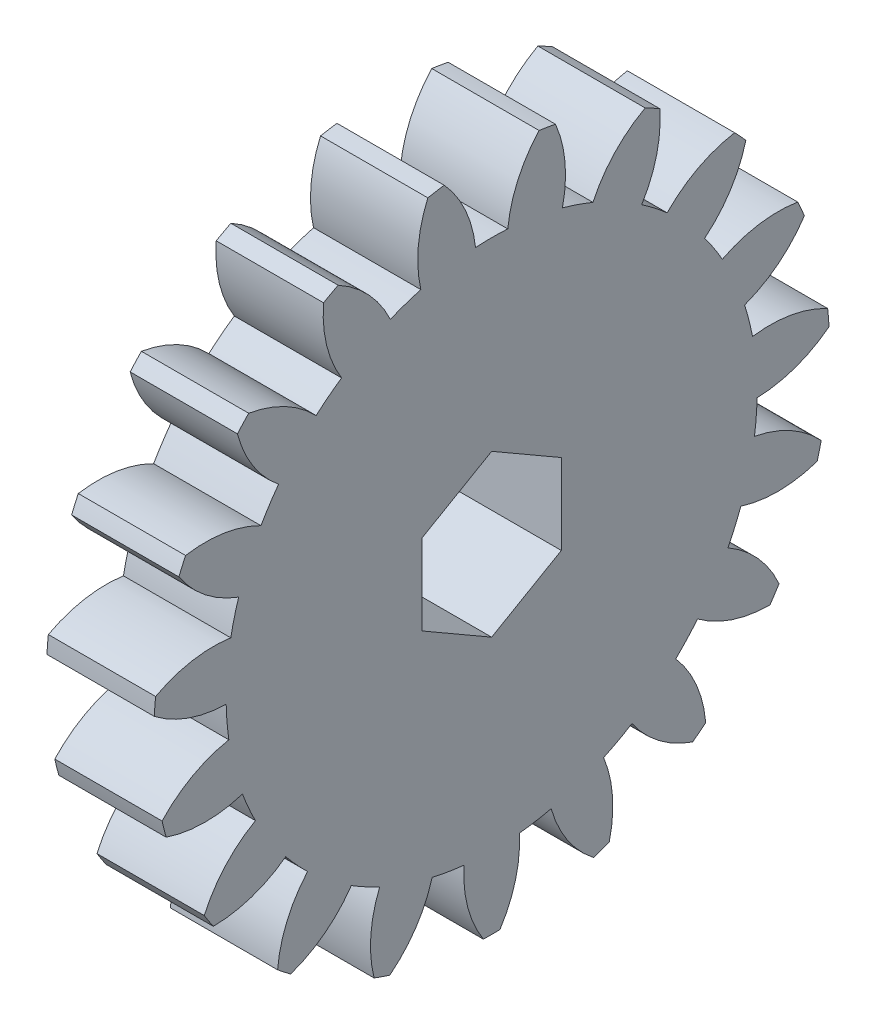
SolidWorks part; units mm, degrees
ref_plane "Plane1" through (0, 0, 0) normal (0, 0, 1) x (1, 0, 0)
ref_plane "Plane2" through (0, 0, 0) normal (0, 1, 0) x (1, 0, 0)
ref_plane "Plane3" through (0, 0, 0) normal (1, 0, 0) x (0, 0, -1)
sketch "HoldingSke" plane through (0, 0, 0) normal (0, 1, 0) x (1, 0, 0)
  line L0 (0, 0) -> (0.6303, -0.217)
  line L1 (-15, 0) -> (100, 0) construction
  line L2 (0, 0) -> (-2.1039, 2.3779)
  line L3 (0, 0) -> (-11.863, 4.5341)
  line L4 (0, 0) -> (8.1655, 2.8116)
  line L5 (0, 0) -> (-46.8476, -17.4728)
  line L6 (0, 0) -> (-4.1448, -2.7965)
  line L7 (-2.1039, 2.3779) -> (8.6586, 51.2059)
  line L8 (-76.2, 54.61) -> (-75.3, 54.61)
  line L9 (-71.009, 38.7566) -> (-53.1078, 45.2721)
  line L10 (-76.2, 71.12) -> (104.1128, 71.12)
  line L11 (0, 0) -> (-5, 0)
  line L12 (-76.2, 101.6) -> (-76.147, 101.6)
  line L13 (24.9733, 27.94) -> (52.9518, 28.4284)
  line L14 (24.9733, 27.94) -> (24.9743, 27.94)
  line L15 (24.9733, 27.94) -> (100.4006, 29.5858)
  line L16 (-63.627, -1.5) -> (-12.827, -1.5)
  circle A0 centre (0, 0) radius 2.5
  circle A1 centre (0, 0) radius 12.374
  circle A2 centre (0, 0) radius 37.5
  circle A3 centre (0, 0) radius 2.5
  dimension "MHD" = 24.748
  dimension "Hub_dia" = 75
  dimension "Bore" = 5
  dimension "MBD" = 5
  dimension "Num_teeth" = 19
  dimension "Pitch" = 0.6667
  dimension "Overall_len" = 50
  dimension "Show_teeth" = 19
  dimension "Thickness" = 5
  dimension "OAL" = 50.0001
  dimension "T_dim" = 0.9
  dimension "Ap" = 20
  dimension "H" = 19.05
  dimension "Pitch_radius" = 180.3128
  dimension "Width" = 5
  dimension "Backlash" = 0.053
  dimension "Addendum_fac" = 1
  dimension "Dedendum_fac" = 1.25
  dimension "Clearance_fac" = 0.25
  dimension "Dedendum_add" = 0.001
  dimension "Module" = 1.5
sketch "BasProSke" plane through (0, 0, 0) normal (0, 1, 0) x (1, 0, 0)
  line L0 (-10, 0) -> (60, 0) construction
  line L1 (0, 0) -> (0, 15.75)
  line L2 (0, 0) -> (5, 0)
  line L3 (5, 0) -> (5, 15.75)
  line L4 (5, 15.75) -> (0, 15.75)
  dimension "Thickness" = 5
  dimension "Diameter" = 31.5
revolve "Base-Revolve" add sketch "BasProSke" angle 360 about L0
sketch "TooCutSke" plane through (0, 0, 0) normal (1, 0, 0) x (0, 0, -1)
  line L1 (0, 0) -> (0, 107) construction
  line L2 (0, 0) -> (-1.2695, 14.1933) construction
  line L3 (0, 0) -> (-4.6774, 28.0298) construction
  line L4 (-1.2695, 14.1933) -> (-2.3387, 14.0149) construction
  arc A0 (0.7515, 12.3512) -> (-0.7515, 12.3512) centre (0, 0) ccw
  arc A1 (2.2309, 15.6169) -> (-2.2309, 15.6169) centre (0, 0) ccw
  circle A2 centre (0, 0) radius 14.25 construction
  circle A3 centre (0, 0) radius 13.3906 construction
  arc A4 (-0.7515, 12.3512) -> (-2.2309, 15.6169) centre (-6.4199, 11.7513) ccw
  arc A5 (2.2309, 15.6169) -> (0.7515, 12.3512) centre (6.4199, 11.7513) ccw
  dimension "Root_dia" = 24.748
  dimension "Overcut_dia" = 31.5508
  dimension "Pitch_dia" = 28.5
  dimension "Base_dia" = 26.7812
  dimension "Flank_rad" = 5.7
  dimension "Half_ang" = 9.474
  dimension "Half_CT" = 1.084
extrude "ToothCut" cut sketch "TooCutSke" along normal through all
fillet "Breaks" [suppressed] radius 0.03
fillet "RootFillets" [suppressed] radius 0.376
pattern_circular "TeethCuts" count 19 every 18.947 about axis through (-10, 0, 0) along (1, 0, 0) of "ToothCut", "RootFillets", "Breaks"
sketch "HubNeaOneSke" plane through (0, 0, 0) normal (-1, 0, 0) x (0, 0, 1)
  circle A0 centre (0, 0) radius 12.374
  dimension "Diameter" = 24.748
extrude "HubNearOne" [suppressed] add sketch "HubNeaOneSke" along normal blind 45.0001
sketch "HubNeaBotSke" plane through (0, 0, 0) normal (-1, 0, 0) x (0, 0, 1)
  circle A0 centre (0, 0) radius 12.374
  dimension "Diameter" = 24.748
extrude "HubNearBoth" [suppressed] add sketch "HubNeaBotSke" along normal blind 22.5
ref_plane "FarPln" through (5, 0, 0) normal (1, 0, 0) x (0, 0, -1)
sketch "HubFarSke" plane through (5, 0, 0) normal (1, 0, 0) x (0, 0, -1)
  circle A0 centre (0, 0) radius 12.374
  dimension "Diameter" = 24.748
extrude "HubFar" [suppressed] add sketch "HubFarSke" along normal blind 22.5
sketch "BorSke" plane through (0, 0, 0) normal (1, 0, 0) x (0, 0, -1)
  line L1 (0, 3.75) -> (-3.2476, 1.875)
  line L2 (-3.2476, 1.875) -> (-3.2476, -1.875)
  line L3 (-3.2476, -1.875) -> (0, -3.75)
  line L4 (0, -3.75) -> (3.2476, -1.875)
  line L5 (3.2476, -1.875) -> (3.2476, 1.875)
  line L6 (3.2476, 1.875) -> (0, 3.75)
  circle A0 centre (0, 0) radius 3.75 construction
  circle A1 centre (0, 0) radius 3.2476 construction
  dimension "Diameter" = 7.5
extrude "Bore" cut sketch "BorSke" along normal mid plane 100.0001
sketch "KeySke" plane through (0, 0, 0) normal (1, 0, 0) x (0, 0, -1)
  line L0 (-1, 0) -> (-1, 3.4)
  line L1 (-1, 3.4) -> (1, 3.4)
  line L2 (1, 3.4) -> (1, 0)
  line L3 (0, 0) -> (0, 34) construction
  line L4 (-1, 0) -> (1, 0)
  dimension "Offset" = 3.4
  dimension "Width" = 2
extrude "Keyway" [suppressed] cut sketch "KeySke" along normal mid plane 100.0001
pattern_circular "Keyway2" [suppressed] count 2 every 90 about axis through (-10, 0, 0) along (1, 0, 0)
equation "' \"Module@HoldingSke\" = 6.35"
equation "' \"Num_teeth@HoldingSke\" = 12"
equation "' \"Ap@HoldingSke\" =  20"
equation "' \"Ap@HoldingSke\" = 20"
equation "' \"Width@HoldingSke\" = 0.5 * 25.4"
equation "' \"Hub_dia@HoldingSke\"= 1 * 25.4"
equation "' \"Hub_dia@HoldingSke\" = 1 * 25.4"
equation "' \"Overall_len@HoldingSke\" = 1.0 * 25.4"
equation "' \"Bore@HoldingSke\" = 0.75 * 25.4"
equation "' \"T_dim@HoldingSke\" = 0.1 * 25.4"
equation "' \"Width@KeySke\" = 0.25 * 25.4"
equation "' \"Show_teeth@HoldingSke\" = 13"
equation "' \"Backlash@HoldingSke\" = 0.009 * 25.4"
equation "' \"Addendum_fac@HoldingSke\" = 1.0"
equation "' \"Dedendum_fac@HoldingSke\" = 1.25"
equation "' \"Dedendum_add@HoldingSke\" = 0.00005 * 25.4"
equation "' \"Clearance_fac@HoldingSke\" = 0.25"
equation "\"Pitch@HoldingSke\" = 1 / \"Module@HoldingSke\""
equation "\"Overcut_dia@TooCutSke\" = (\"Num_teeth@HoldingSke\" + 2 * \"Addendum_fac@HoldingSke\") / \"Pitch@HoldingSke\" + 0.002 * 25.4"
equation "\"Pitch_dia@TooCutSke\" = \"Num_teeth@HoldingSke\" / \"Pitch@HoldingSke\""
equation "\"Base_dia@TooCutSke\" = \"Num_teeth@HoldingSke\" / \"Pitch@HoldingSke\" * cos((\"Ap@HoldingSke\"  * 3.14159265 / 180))"
equation "\"Root_dia@TooCutSke\" = (\"Num_teeth@HoldingSke\" + 2) / \"Pitch@HoldingSke\" - 2 * (\"Addendum_fac@HoldingSke\" + \"Dedendum_fac@HoldingSke\") / \"Pitch@HoldingSke\" - \"Dedendum_add@HoldingSke\" * 2"
equation "\"Half_ang@TooCutSke\" = 180 / \"Num_teeth@HoldingSke\""
equation "\"Half_CT@TooCutSke\" = \"Num_teeth@HoldingSke\" / \"Pitch@HoldingSke\" * sin((3.14159265 / 2 / \"Num_teeth@HoldingSke\")) / 2 - 7 * \"Backlash@HoldingSke\" / 4"
equation "\"Flank_rad@TooCutSke\" = \"Num_teeth@HoldingSke\" / \"Pitch@HoldingSke\" / 5"
equation "\"Radius@RootFillets\" = \"Clearance_fac@HoldingSke\" / \"Pitch@HoldingSke\" + \"Dedendum_add@HoldingSke\""
equation "\"Break_rad@Breaks\" = 0.02 / \"Pitch@HoldingSke\""
equation "\"Thickness@HoldingSke\" = \"Width@HoldingSke\""
equation "\"OAL@HoldingSke\" = \"Thickness@HoldingSke\""
equation "\"MHD@HoldingSke\" = (\"Num_teeth@HoldingSke\" + 2) / \"Pitch@HoldingSke\" - 2 * (\"Addendum_fac@HoldingSke\" + \"Dedendum_fac@HoldingSke\")  / \"Pitch@HoldingSke\" - \"Dedendum_add@HoldingSke\" * 2"
equation "\"MBD@HoldingSke\" = (\"Num_teeth@HoldingSke\" + 2) / \"Pitch@HoldingSke\" - 2 * (\"Addendum_fac@HoldingSke\" + \"Dedendum_fac@HoldingSke\")  / \"Pitch@HoldingSke\" - \"Dedendum_add@HoldingSke\" * 2 - 0.002 * 25.4"
equation "\"MHD@HoldingSke\" = ((sgn( \"MHD@HoldingSke\" - \"Hub_dia@HoldingSke\" )-1)*( \"MHD@HoldingSke\" - \"Hub_dia@HoldingSke\" ))/-2+ \"Hub_dia@HoldingSke\""
equation "\"MBD@HoldingSke\" = ((sgn( \"MBD@HoldingSke\" - \"Bore@HoldingSke\" )-1)*( \"MBD@HoldingSke\" - \"Bore@HoldingSke\" ))/-2+ \"Bore@HoldingSke\""
equation "\"OAL@HoldingSke\" = ((sgn( \"OAL@HoldingSke\" - \"Overall_len@HoldingSke\" )+1)*( \"OAL@HoldingSke\" - \"Overall_len@HoldingSke\" ))/2 + \"Overall_len@HoldingSke\" + 0.000002 * 25.4"
equation "\"Num_teeth@TeethCuts\" = int( \"Show_teeth@HoldingSke\" ) + 1"
equation "\"Num_teeth@TeethCuts\" = ((sgn( \"Num_teeth@TeethCuts\" - \"Num_teeth@HoldingSke\" )-1)*( \"Num_teeth@TeethCuts\" - \"Num_teeth@HoldingSke\" ))/-2+ \"Num_teeth@HoldingSke\""
equation "\"Num_teeth@TeethCuts\" = ((sgn( \"Num_teeth@TeethCuts\" - 2.0)+1)*( \"Num_teeth@TeethCuts\" - 2.0))/2 +2.0"
equation "\"Angle@TeethCuts\" = 360.0 / \"Num_teeth@HoldingSke\""
equation "\"Diameter@BasProSke\" = (\"Num_teeth@HoldingSke\" + 2 * \"Addendum_fac@HoldingSke\") / \"Pitch@HoldingSke\""
equation "\"Thickness@BasProSke\"  = \"Thickness@HoldingSke\""
equation "' \"Fillet_rad@BasProSke\" =  \"Thickness@HoldingSke\" * 0.05"
equation "' \"Fillet_rad@BasProSke\" = \"Thickness@HoldingSke\" * 0.05"
equation "\"MHD@HoldingSke\" = ((sgn( \"MHD@HoldingSke\" - \"Root_dia@TooCutSke\" )-1)*( \"MHD@HoldingSke\" - \"Root_dia@TooCutSke\" ))/-2+ \"Root_dia@TooCutSke\""
equation "\"Diameter@HubNeaOneSke\" = \"MHD@HoldingSke\""
equation "\"Length@HubNearOne\" = \"OAL@HoldingSke\" - \"Thickness@BasProSke\""
equation "\"Diameter@HubNeaBotSke\" = \"MHD@HoldingSke\""
equation "\"Length@HubNearBoth\" = ( \"OAL@HoldingSke\" - \"Thickness@BasProSke\" ) / 2.0"
equation "\"Thickness@FarPln\" = \"Thickness@BasProSke\""
equation "\"Diameter@HubFarSke\" = \"MHD@HoldingSke\""
equation "\"Length@HubFar\" = ( \"OAL@HoldingSke\" - \"Thickness@BasProSke\" ) / 2.0"
equation "\"D1@Bore\" = \"OAL@HoldingSke\" * 2.0"
equation "\"D1@Keyway\" = \"OAL@HoldingSke\" * 2.0"
equation "\"Offset@KeySke\" = \"T_dim@HoldingSke\" + \"MBD@HoldingSke\" / 2.0"
